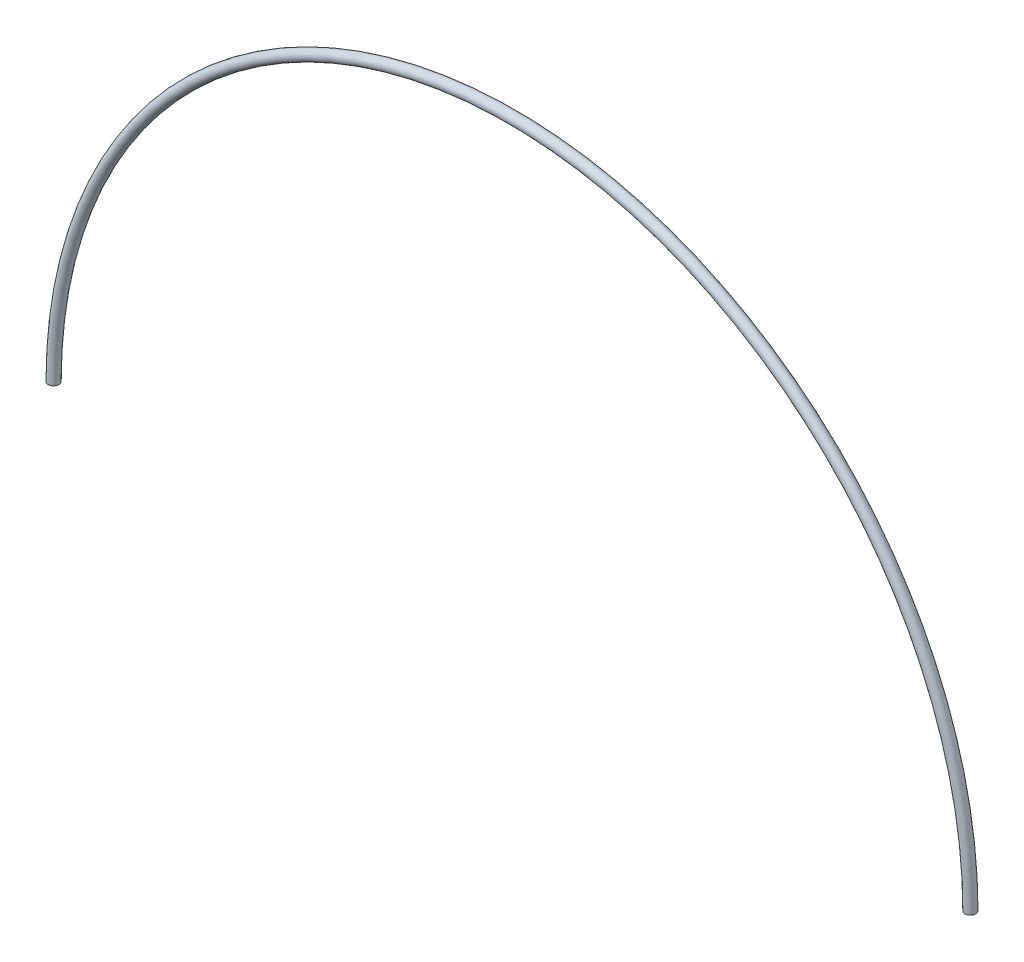
SolidWorks part; units mm, degrees
ref_plane "Front" through (0, 0, 0) normal (0, 0, 1) x (1, 0, 0)
ref_plane "Top" through (0, 0, 0) normal (0, 1, 0) x (1, 0, 0)
ref_plane "Right" through (0, 0, 0) normal (1, 0, 0) x (0, 0, -1)
sketch "Sketch1" plane through (0, 0, 0) normal (0, 0, 1) x (1, 0, 0)
  line L0 (419.1, 0) -> (-419.1, 0) construction
  arc A0 (-406.4, 0) -> (406.4, 0) centre (0, 0) cw
  dimension "D1" = 406.4
ref_plane "Plane1" through (406.4, 0, 0) normal (0, -1, 0) x (1, 0, 0)
sketch "Sketch2" plane through (406.4, 0, 0) normal (0, -1, 0) x (1, 0, 0)
  line L0 (0, -12.7) -> (0, 12.7) construction
  circle A0 centre (0, 0) radius 4.7625
  dimension "D1" = 9.525
sweep "Sweep1" add profiles "Sketch2" path "Sketch1"
